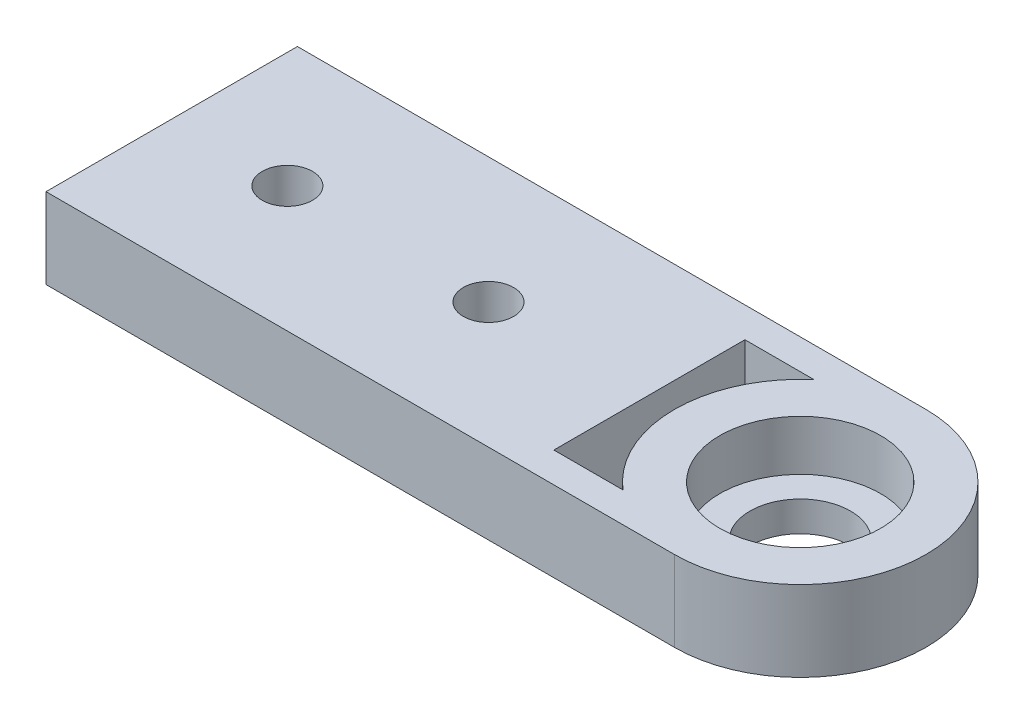
SolidWorks part; units mm, degrees
ref_plane "Front Plane" through (0, 0, 0) normal (0, 0, 1) x (1, 0, 0)
ref_plane "Top Plane" through (0, 0, 0) normal (0, 1, 0) x (1, 0, 0)
ref_plane "Right Plane" through (0, 0, 0) normal (1, 0, 0) x (0, 0, -1)
sketch "Sketch1" plane through (0, 0, 0) normal (0, 1, 0) x (1, 0, 0)
  line L0 (0, 0) -> (-16.25, 0) construction
  line L1 (-16.25, 12.5) -> (16.25, 12.5)
  line L2 (-16.25, 12.5) -> (-16.25, -12.5)
  line L3 (-16.25, -12.5) -> (16.25, -12.5)
  line L4 (16.25, 9.5) -> (16.25, -9.5)
  line L5 (-16.25, 12.5) -> (0, 0) construction
  line L6 (-16.25, -12.5) -> (16.25, 12.5) construction
  line L7 (-16.25, 0) -> (31.25, 0) construction
  line L8 (16.25, 12.5) -> (31.25, 12.5)
  line L10 (23.126, 9.5) -> (16.25, 9.5)
  line L12 (16.25, -12.5) -> (31.25, -12.5)
  line L14 (23.126, -9.5) -> (16.25, -9.5)
  line L15 (-16.25, 0) -> (-1.25, 0) construction
  arc A0 (23.126, 9.5) -> (23.126, -9.5) centre (31.25, 0) ccw
  arc A1 (31.25, -12.5) -> (31.25, 12.5) centre (31.25, 0) ccw
  circle A2 centre (31.25, 0) radius 5
  point P0 (0, 0)
  dimension "D4" = 25
  dimension "D5" = 10
  dimension "D1" = 32.5
  dimension "D2" = 25
  dimension "D3" = 47.5
  dimension "D6" = 15
extrude "Boss-Extrude1" add sketch "Sketch1" along normal blind 8
sketch "Sketch2" plane through (0, 8, 0) normal (0, 1, 0) x (1, 0, 0)
  circle A0 centre (31.25, 0) radius 8
  dimension "D1" = 16
extrude "Cut-Extrude1" cut sketch "Sketch2" against normal blind 5
sketch "Sketch3" plane through (-16.25, 0, 0) normal (-1, 0, 0) x (0, 0, 1)
  line L1 (-12.5, 0) -> (12.5, 0)
  line L2 (-12.5, 0) -> (-12.5, 8)
  line L3 (-12.5, 8) -> (12.5, 8)
  line L4 (12.5, 0) -> (12.5, 8)
extrude "Boss-Extrude2" add sketch "Sketch3" along normal blind 15
sketch "Sketch4" plane through (0, 0, 0) normal (0, -1, 0) x (-1, 0, 0)
  line L0 (-0.25, 52.1366) -> (-0.25, -6.0551) construction
  line L1 (-3.25, 52.1366) -> (2.75, 52.1366) construction
  line L2 (19.75, 52.1366) -> (19.75, -7.5429) construction
  line L3 (16.75, 52.1366) -> (22.75, 52.1366) construction
  line L4 (-16.25, 0) -> (31.25, 0) construction
  line L5 (-16.25, 9.5) -> (-16.25, -9.5) construction
  line L6 (31.25, 12.5) -> (31.25, -12.5) construction
  circle A0 centre (-0.25, 0) radius 2.5
  circle A1 centre (19.75, 0) radius 2.5
  dimension "D1" = 5
  dimension "D2" = 5
extrude "Cut-Extrude2" cut sketch "Sketch4" against normal blind 10
